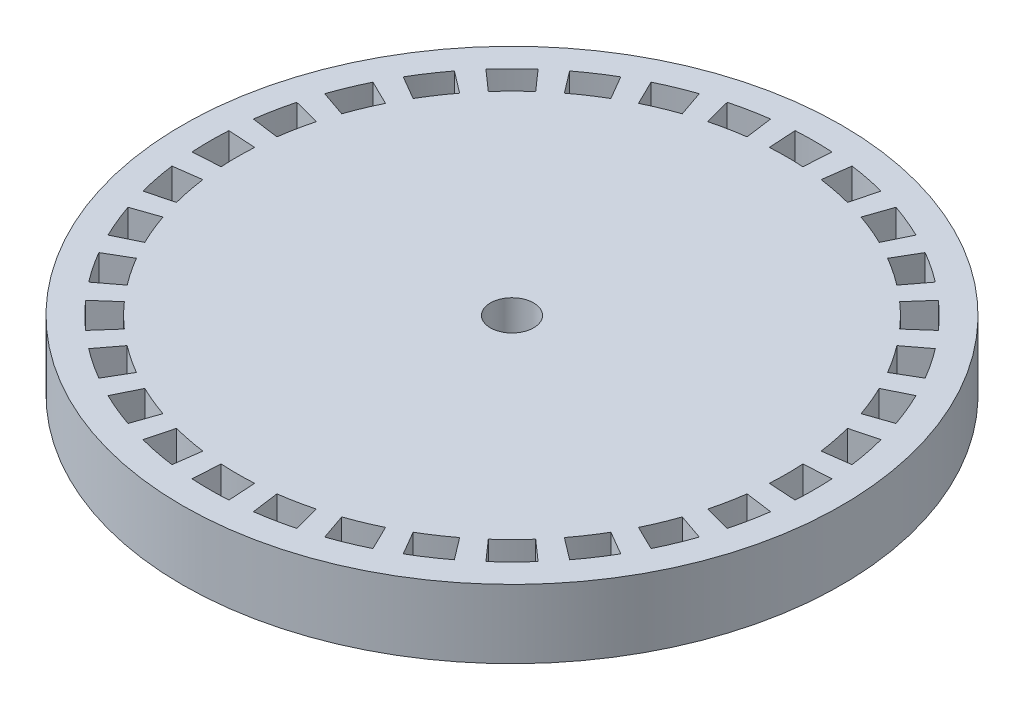
SolidWorks part; units mm, degrees
ref_plane "Front Plane" through (0, 0, 0) normal (0, 0, 1) x (1, 0, 0)
ref_plane "Top Plane" through (0, 0, 0) normal (0, 1, 0) x (1, 0, 0)
ref_plane "Right Plane" through (0, 0, 0) normal (1, 0, 0) x (0, 0, -1)
sketch "Sketch2" plane through (0, 0, 0) normal (0, 1, 0) x (1, 0, 0)
  circle A0 centre (0, 0) radius 76.2
  circle A1 centre (0, 0) radius 5
  dimension "D1" = 152.4
  dimension "D2" = 10
extrude "Boss-Extrude1" add sketch "Sketch2" along normal blind 15.875
sketch "Sketch3" plane through (0, 15.875, 0) normal (0, 1, 0) x (1, 0, 0)
  line L0 (-4.2642, 69.7197) -> (-3.8766, 63.3816)
  line L1 (3.8766, 63.3816) -> (4.2642, 69.7197)
  line L2 (0, 69.85) -> (0, 0) construction
  arc A0 (-4.2642, 69.7197) -> (4.2642, 69.7197) centre (0, 0) cw
  arc A1 (-3.8766, 63.3816) -> (3.8766, 63.3816) centre (0, 0) cw
  point P10 (0, 63.5)
  dimension "D2" = 69.85
  dimension "D3" = 6.35
  dimension "D1" = 7
extrude "Cut-Extrude1" cut sketch "Sketch3" against normal through all contours A1 L1 A0 L0
pattern_circular "CirPattern1" count 32 over 360 about axis through (0, 0, 0) along (0, 1, 0) of "Cut-Extrude1"
